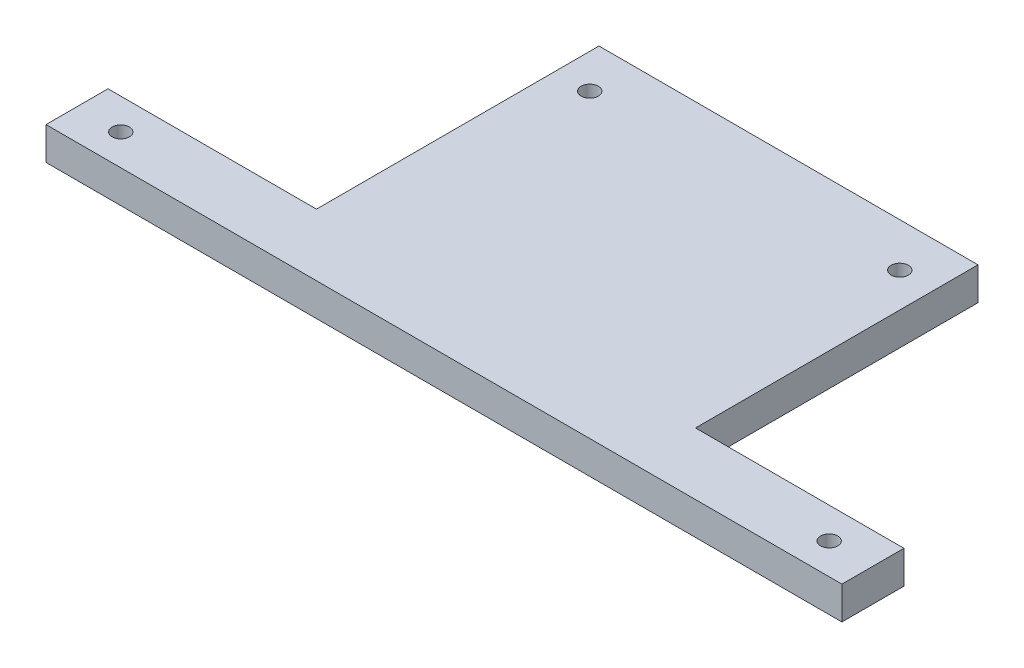
SolidWorks part; units mm, degrees
ref_plane "Front Plane" through (0, 0, 0) normal (0, 0, 1) x (1, 0, 0)
ref_plane "Top Plane" through (0, 0, 0) normal (0, 1, 0) x (1, 0, 0)
ref_plane "Right Plane" through (0, 0, 0) normal (1, 0, 0) x (0, 0, -1)
sketch "Sketch1" plane through (0, 0, 0) normal (0, 1, 0) x (1, 0, 0)
  line L0 (-55, -1) -> (-55, 81)
  line L1 (-55, 81) -> (55, 81)
  line L2 (55, 81) -> (55, -1)
  line L3 (55, -1) -> (115.5, -1)
  line L4 (115.5, -1) -> (115.5, -19)
  line L5 (115.5, -19) -> (-115.5, -19)
  line L6 (-115.5, -19) -> (-115.5, -1)
  line L7 (-115.5, -1) -> (-55, -1)
  point P8 (0, 81)
  dimension "D1" = 18
  dimension "D2" = 18
  dimension "D3" = 231
  dimension "D4" = 100
  dimension "D5" = 110
extrude "Boss-Extrude1" add sketch "Sketch1" along normal mid plane 9.525
hole_wizard "Tap Drill for M6x1.0 Tap1" positions "Sketch3" profile "Sketch2" hole size "M6x1.0" standard "ANSI Metric" end condition up to next
sketch "Sketch3" plane through (0, 4.7625, 0) normal (0, 1, 0) x (1, 0, 0)
  line L0 (-55, 81) -> (-55, -1) construction
  line L1 (55, -1) -> (55, 81) construction
  line L2 (55, 81) -> (-55, 81) construction
  line L5 (-55, -1) -> (-115.5, -1) construction
  line L6 (115.5, -1) -> (55, -1) construction
  line L7 (-115.5, -1) -> (-115.5, -19) construction
  line L8 (115.5, -19) -> (115.5, -1) construction
  point P0 (-45, 68.3)
  point P2 (45, 68.3)
  point P4 (-102.8, -10)
  point P6 (102.8, -10)
  dimension "D1" = 10
  dimension "D2" = 10
  dimension "D3" = 12.7
  dimension "D4" = 12.7
  dimension "D5" = 9
  dimension "D6" = 9
  dimension "D7" = 12.7
  dimension "D8" = 12.7
sketch "Sketch2" plane through (-45, 4.7625, -68.3) normal (1, 0, 0) x (0, 0, 1)
  line L0 (0, 0) -> (0, 9.525)
  line L1 (0, 9.525) -> (2.5, 9.525)
  line L2 (2.5, 9.525) -> (2.5, 0)
  line L5 (2.5, 0) -> (0, 0)
  line L11 (0, -6.35) -> (0, 107.95) construction
  dimension "Thru Hole Dia." = 5
  dimension "Thru Hole Depth" = 9.525
